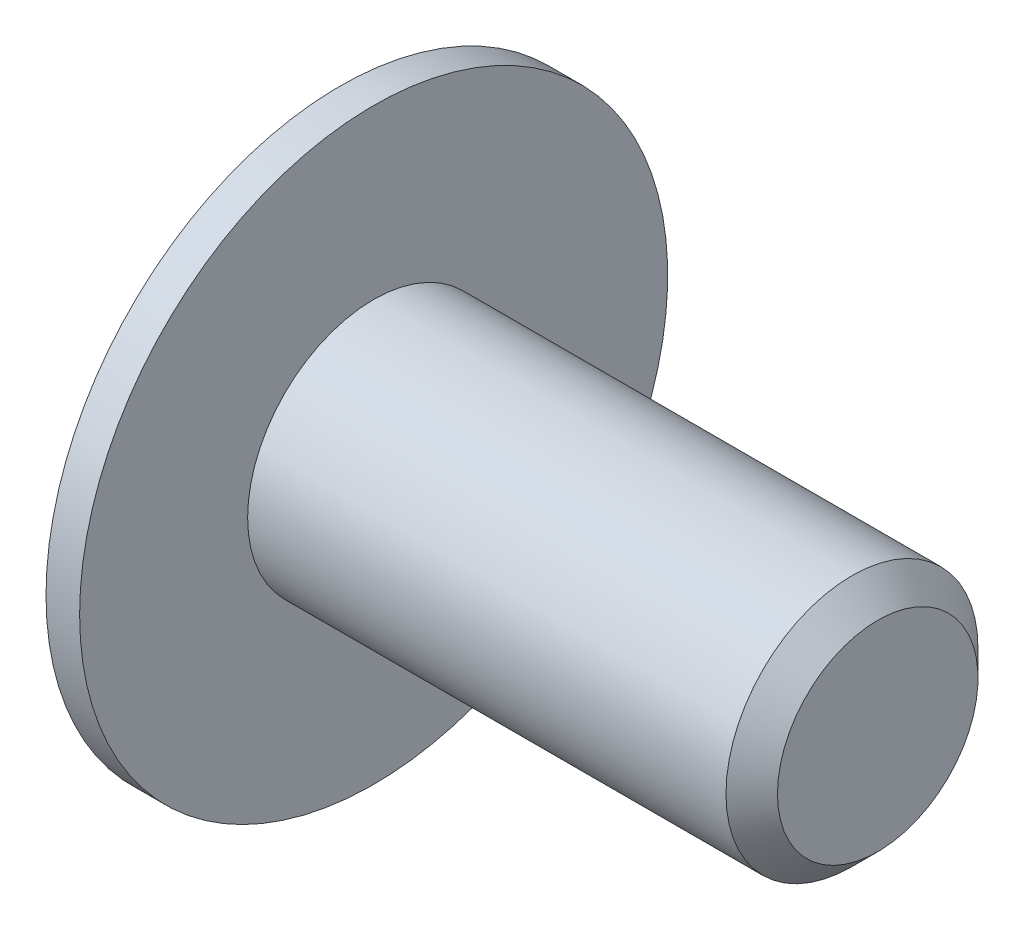
SolidWorks part; units mm, degrees
ref_plane "Front Plane" through (0, 0, 0) normal (0, 0, 1) x (1, 0, 0)
ref_plane "Top Plane" through (0, 0, 0) normal (0, 1, 0) x (1, 0, 0)
ref_plane "Right Plane" through (0, 0, 0) normal (1, 0, 0) x (0, 0, -1)
ref_plane "Plane1" through (0, 0, 0) normal (0, 0, 1) x (1, 0, 0)
sketch "Sketch1" plane through (0, 0, 0) normal (0, 0, 1) x (1, 0, 0)
  line L0 (-0.8, 0) -> (-0.8, 2.8)
  line L1 (-0.8, 2.8) -> (-0.4, 3.5)
  line L2 (-0.4, 3.5) -> (0, 3.5)
  line L3 (0, 3.5) -> (0, 1.5)
  line L4 (0, 1.5) -> (5.6935, 1.5)
  line L5 (5.6935, 1.5) -> (6, 1.1935)
  line L6 (6, 1.1935) -> (6, 0)
  line L7 (6, 0) -> (-0.8, 0)
  line L8 (6, 0) -> (-0.8, 0) construction
revolve "Revolve1" add sketch "Sketch1" angle 360 about L8
cosmetic thread "Cosmetic Thread1" parameters "D1"=5.6, "D2"=2.387
ref_plane "Plane2" through (-0.8, 0, 0) normal (1, 0, 0) x (0, 0, -1)
sketch "Sketch2" plane through (-0.8, 0, 0) normal (1, 0, 0) x (0, 0, -1)
  line L0 (-1.1667, 0.2333) -> (-1.1667, -0.2333)
  line L1 (-1.1667, -0.2333) -> (-0.4667, -0.2333)
  line L2 (-0.2333, -0.4667) -> (-0.2333, -1.1667)
  line L3 (-0.2333, -1.1667) -> (0.2333, -1.1667)
  line L4 (0.2333, -1.1667) -> (0.2333, -0.4667)
  line L5 (0.4667, -0.2333) -> (1.1667, -0.2333)
  line L6 (1.1667, -0.2333) -> (1.1667, 0.2333)
  line L7 (1.1667, 0.2333) -> (0.4667, 0.2333)
  line L8 (0.2333, 0.4667) -> (0.2333, 1.1667)
  line L9 (0.2333, 1.1667) -> (-0.2333, 1.1667)
  line L10 (-0.2333, 1.1667) -> (-0.2333, 0.4667)
  line L11 (-0.4667, 0.2333) -> (-1.1667, 0.2333)
  arc A0 (-0.4667, -0.2333) -> (-0.2333, -0.4667) centre (-0.4667, -0.4667) cw
  arc A1 (0.2333, -0.4667) -> (0.4667, -0.2333) centre (0.4667, -0.4667) cw
  arc A2 (0.4667, 0.2333) -> (0.2333, 0.4667) centre (0.4667, 0.4667) cw
  arc A3 (-0.2333, 0.4667) -> (-0.4667, 0.2333) centre (-0.4667, 0.4667) cw
extrude "Cut-Extrude1" cut sketch "Sketch2" along normal blind 0.4
